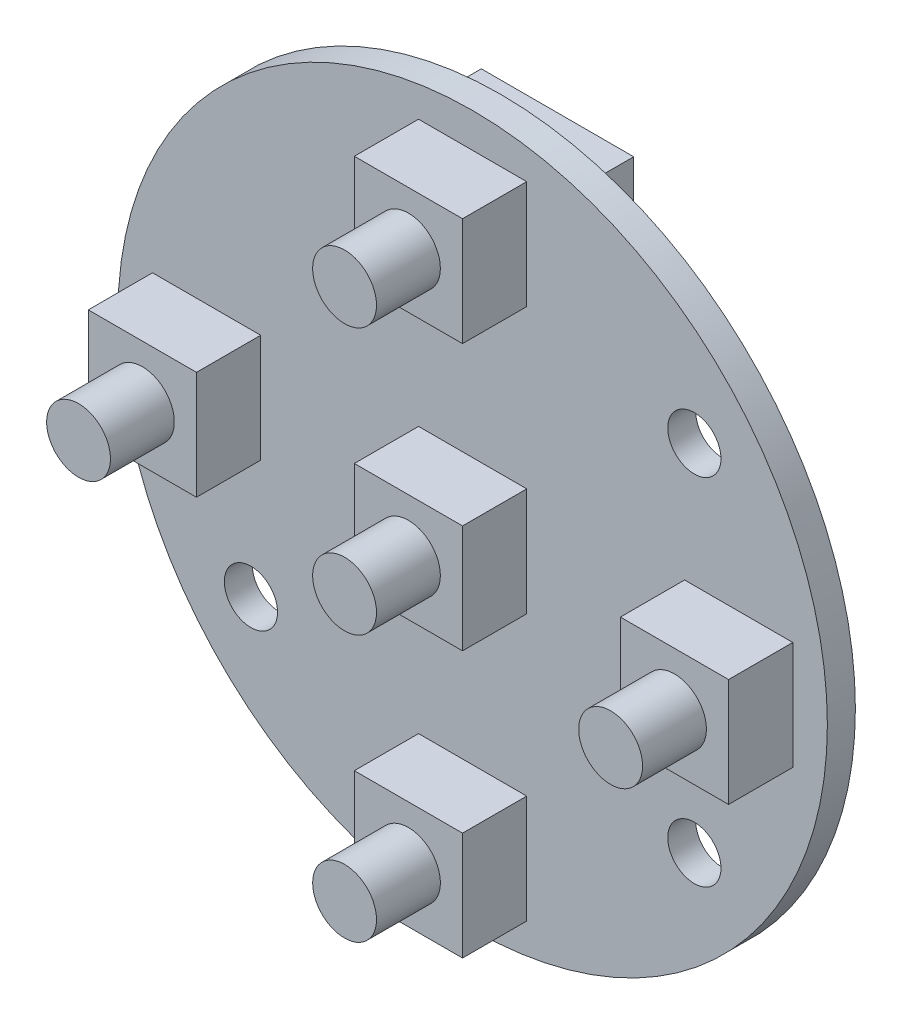
SolidWorks part; units mm, degrees
ref_plane "Plan de face" through (0, 0, 0) normal (0, 0, 1) x (1, 0, 0)
ref_plane "Plan de dessus" through (0, 0, 0) normal (0, 1, 0) x (1, 0, 0)
ref_plane "Plan de droite" through (0, 0, 0) normal (1, 0, 0) x (0, 0, -1)
sketch "Esquisse3" plane through (0, 0, 0) normal (0, 0, 1) x (1, 0, 0)
  line L0 (-130.3842, 0) -> (6388.8247, 0) construction
  line L2 (-18.05, 3.05) -> (-11.95, 3.05)
  line L3 (-18.05, 3.05) -> (-18.05, -3.05)
  line L4 (-18.05, -3.05) -> (-11.95, -3.05)
  line L5 (-11.95, 3.05) -> (-11.95, -3.05)
  line L6 (11.95, 3.05) -> (18.05, 3.05)
  line L7 (11.95, 3.05) -> (11.95, -3.05)
  line L8 (11.95, -3.05) -> (18.05, -3.05)
  line L9 (18.05, 3.05) -> (18.05, -3.05)
  line L10 (-3.05, 18.05) -> (3.05, 18.05)
  line L11 (-3.05, 18.05) -> (-3.05, 11.95)
  line L12 (-3.05, 11.95) -> (3.05, 11.95)
  line L13 (3.05, 18.05) -> (3.05, 11.95)
  line L14 (-3.05, -11.95) -> (3.05, -11.95)
  line L15 (-3.05, -11.95) -> (-3.05, -18.05)
  line L16 (-3.05, -18.05) -> (3.05, -18.05)
  line L17 (3.05, -11.95) -> (3.05, -18.05)
  line L18 (-3.05, -3.05) -> (3.05, -3.05)
  line L19 (-3.05, -3.05) -> (-3.05, 3.05)
  line L20 (-3.05, 3.05) -> (3.05, 3.05)
  line L21 (3.05, -3.05) -> (3.05, 3.05)
  line L22 (-3.05, -3.05) -> (3.05, 3.05) construction
  line L23 (-3.05, 3.05) -> (3.05, -3.05) construction
  circle A0 centre (0, 0) radius 20
  circle A1 centre (-12.5, -10) radius 1.5
  circle A2 centre (12.5, -10) radius 1.5
  circle A3 centre (12.5, 10) radius 1.5
  dimension "D1" = 40
  dimension "D5" = 3
  dimension "D2" = 10
  dimension "D3" = 25
  dimension "D4" = 12.5
  dimension "D6" = 10
  dimension "D7" = 6.1
  dimension "D8" = 3.05
  dimension "D9" = 11.95
  dimension "D10" = 11.95
  dimension "D11" = 11.95
  dimension "D12" = 11.95
  dimension "D13" = 3.05
extrude "Boss.-Extru.2" add sketch "Esquisse3" along normal blind 1.58
sketch "Esquisse5" plane through (0, 0, 0) normal (0, 0, -1) x (-1, 0, 0)
  line L1 (3.05, 18.05) -> (-3.05, 18.05)
  line L2 (3.05, 18.05) -> (3.05, 11.95)
  line L3 (3.05, 11.95) -> (-3.05, 11.95)
  line L4 (-3.05, 18.05) -> (-3.05, 11.95)
  line L5 (-18.05, -3.05) -> (-11.95, -3.05)
  line L6 (-18.05, -3.05) -> (-18.05, 3.05)
  line L7 (-18.05, 3.05) -> (-11.95, 3.05)
  line L8 (-11.95, -3.05) -> (-11.95, 3.05)
  line L9 (11.95, 3.05) -> (18.05, 3.05)
  line L10 (11.95, 3.05) -> (11.95, -3.05)
  line L11 (11.95, -3.05) -> (18.05, -3.05)
  line L12 (18.05, 3.05) -> (18.05, -3.05)
  line L13 (-3.05, -3.05) -> (3.05, -3.05)
  line L14 (-3.05, -3.05) -> (-3.05, 3.05)
  line L15 (-3.05, 3.05) -> (3.05, 3.05)
  line L16 (3.05, -3.05) -> (3.05, 3.05)
  line L17 (-3.05, -11.95) -> (3.05, -11.95)
  line L18 (-3.05, -11.95) -> (-3.05, -18.05)
  line L19 (-3.05, -18.05) -> (3.05, -18.05)
  line L20 (3.05, -11.95) -> (3.05, -18.05)
extrude "Boss.-Extru.3" add sketch "Esquisse5" against normal blind 5.2
sketch "Esquisse6" plane through (0, 0, 5.2) normal (0, 0, 1) x (1, 0, 0)
  circle A0 centre (0, 0) radius 1.8
  circle A1 centre (0, 15) radius 1.8
  circle A2 centre (15, 0) radius 1.8
  circle A3 centre (0, -15) radius 1.8
  circle A4 centre (-15, 0) radius 1.8
  dimension "D5" = 3.6
  dimension "D1" = 15
  dimension "D2" = 15
  dimension "D3" = 15
  dimension "D4" = 15
extrude "Boss.-Extru.4" add sketch "Esquisse6" along normal blind 3.6
sketch "Esquisse7" plane through (0, 0, 0) normal (0, 0, 1) x (1, 0, 0)
  line L1 (-11.01, 10.78) -> (-2.42, 10.78)
  line L2 (-11.01, 10.78) -> (-11.01, -9.52)
  line L3 (-11.01, -9.52) -> (-2.42, -9.52)
  line L4 (-2.42, 10.78) -> (-2.42, -9.52)
  line L5 (-11.01, 10.78) -> (-2.42, -9.52) construction
  line L6 (-11.01, -9.52) -> (-2.42, 10.78) construction
  point P0 (-6.715, 0.63)
  dimension "D1" = 2.42
  dimension "D2" = 10.78
  dimension "D3" = 20.3
  dimension "D4" = 8.59
extrude "Boss.-Extru.5" add sketch "Esquisse7" against normal blind 9.92
